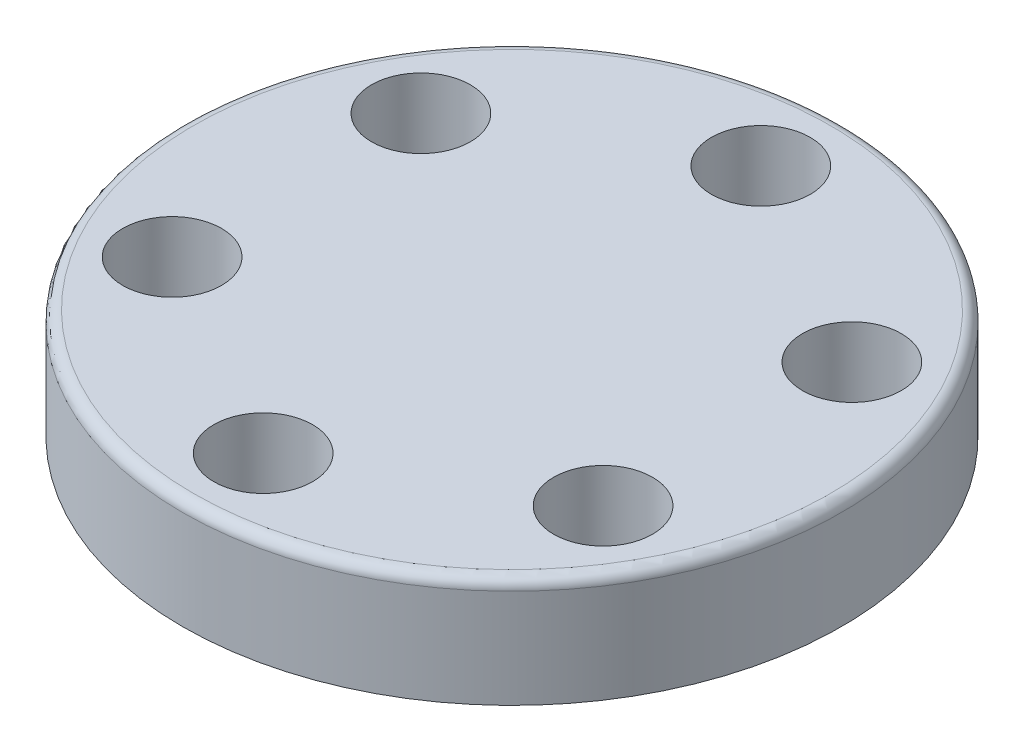
SolidWorks part; units mm, degrees
material "ｼﾘｺﾝ ｺﾞﾑ"
ref_plane "正面" through (0, 0, 0) normal (0, 0, 1) x (1, 0, 0)
ref_plane "平面" through (0, 0, 0) normal (0, 1, 0) x (1, 0, 0)
ref_plane "右側面" through (0, 0, 0) normal (1, 0, 0) x (0, 0, -1)
sketch "ｽｹｯﾁ1" plane through (0, 0, 0) normal (0, 1, 0) x (1, 0, 0)
  circle A0 centre (0, 0) radius 30
  circle A1 centre (0, -22.65) radius 4.5
  circle A2 centre (-19.6155, -11.325) radius 4.5
  circle A3 centre (-19.6155, 11.325) radius 4.5
  circle A4 centre (0, 22.65) radius 4.5
  circle A5 centre (19.6155, 11.325) radius 4.5
  circle A6 centre (19.6155, -11.325) radius 4.5
  point P18 (0, 0)
  dimension "D1" = 6
extrude "ﾎﾞｽ - 押し出し2" add sketch "ｽｹｯﾁ1" along normal blind 10
sketch "ｽｹｯﾁ3" plane through (0, 0, 0) normal (0, -1, 0) x (1, 0, 0)
  circle A0 centre (-19.6155, -11.325) radius 4.5
  circle A1 centre (-19.6155, -11.325) radius 2.5
  circle A2 centre (-19.6155, 11.325) radius 2.5
  circle A3 centre (-19.6155, 11.325) radius 4.5
  circle A4 centre (0, 22.65) radius 2.5
  circle A5 centre (0, 22.65) radius 4.5
  circle A6 centre (19.6155, 11.325) radius 2.5
  circle A7 centre (19.6155, 11.325) radius 4.5
  circle A8 centre (19.6155, -11.325) radius 2.5
  circle A9 centre (19.6155, -11.325) radius 4.5
  circle A10 centre (0, -22.65) radius 2.5
  circle A11 centre (0, -22.65) radius 4.5
  point P22 (0, 0)
  dimension "D1" = 6
extrude "ﾎﾞｽ - 押し出し3" add sketch "ｽｹｯﾁ3" against normal blind 3
fillet "ﾌｨﾚｯﾄ1" radius 1 1 edges at (0, 10, 30)
